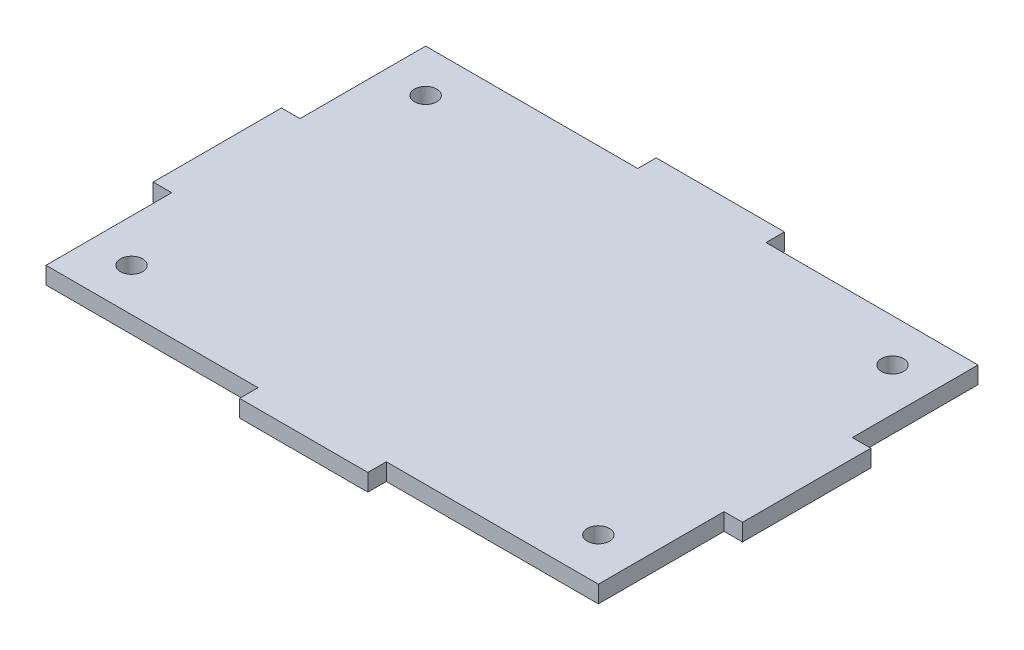
SolidWorks part; units mm, degrees
ref_plane "Front Plane" through (0, 0, 0) normal (0, 0, 1) x (1, 0, 0)
ref_plane "Top Plane" through (0, 0, 0) normal (0, 1, 0) x (1, 0, 0)
ref_plane "Right Plane" through (0, 0, 0) normal (1, 0, 0) x (0, 0, -1)
sketch "Sketch1" plane through (0, 0, 0) normal (0, 1, 0) x (1, 0, 0)
  line L1 (41.021, -28.194) -> (-41.021, -28.194)
  line L2 (41.021, -28.194) -> (41.021, 28.194)
  line L3 (41.021, 28.194) -> (-41.021, 28.194)
  line L4 (-41.021, -28.194) -> (-41.021, 28.194)
  line L5 (41.021, -28.194) -> (-41.021, 28.194) construction
  line L6 (41.021, 28.194) -> (-41.021, -28.194) construction
  line L7 (-34.671, 21.844) -> (34.671, 21.844) construction
  line L8 (-34.671, 21.844) -> (-34.671, -21.844) construction
  line L9 (-34.671, -21.844) -> (34.671, -21.844) construction
  line L10 (34.671, 21.844) -> (34.671, -21.844) construction
  line L11 (-34.671, 21.844) -> (34.671, -21.844) construction
  line L12 (-34.671, -21.844) -> (34.671, 21.844) construction
  circle A0 centre (-34.671, 21.844) radius 1.651
  circle A1 centre (-34.671, -21.844) radius 1.651
  circle A2 centre (34.671, -21.844) radius 1.651
  circle A3 centre (34.671, 21.844) radius 1.651
  point P0 (0, 0)
  point P6 (0, 0)
  dimension "D1" = 3.302
  dimension "D2" = 43.688
  dimension "D3" = 69.342
  dimension "D4" = 6.35
  dimension "D5" = 6.35
  dimension "D6" = 82.042
  dimension "D7" = 56.388
extrude "Boss-Extrude1" add sketch "Sketch1" along normal blind 2.54
sketch "Sketch2" plane through (0, 2.54, 0) normal (0, 1, 0) x (1, 0, 0)
  line L0 (41.021, 28.194) -> (-41.021, 28.194) construction
  line L1 (9.525, 28.194) -> (-9.525, 28.194)
  line L2 (9.525, 28.194) -> (9.525, 30.9372)
  line L3 (9.525, 30.9372) -> (-9.525, 30.9372)
  line L4 (-9.525, 28.194) -> (-9.525, 30.9372)
  line L5 (-41.021, -28.194) -> (41.021, -28.194) construction
  line L6 (-9.525, -28.194) -> (9.525, -28.194)
  line L7 (-9.525, -28.194) -> (-9.525, -30.9372)
  line L8 (-9.525, -30.9372) -> (9.525, -30.9372)
  line L9 (9.525, -28.194) -> (9.525, -30.9372)
  line L10 (41.021, -28.194) -> (41.021, 28.194) construction
  line L11 (41.021, 9.525) -> (43.7642, 9.525)
  line L12 (41.021, 9.525) -> (41.021, -9.525)
  line L13 (41.021, -9.525) -> (43.7642, -9.525)
  line L14 (43.7642, 9.525) -> (43.7642, -9.525)
  line L15 (-41.021, 28.194) -> (-41.021, -28.194) construction
  line L16 (-41.021, 9.525) -> (-43.7642, 9.525)
  line L17 (-41.021, 9.525) -> (-41.021, -9.525)
  line L18 (-41.021, -9.525) -> (-43.7642, -9.525)
  line L19 (-43.7642, 9.525) -> (-43.7642, -9.525)
  line L20 (0, 30.9372) -> (0, -30.9372) construction
  line L21 (-43.7642, 0) -> (43.7642, 0) construction
  dimension "D1" = 2.7432
  dimension "D2" = 19.05
extrude "Boss-Extrude2" add sketch "Sketch2" against normal up to surface (2.54 mm away) up to face at (0, 0, 0)
